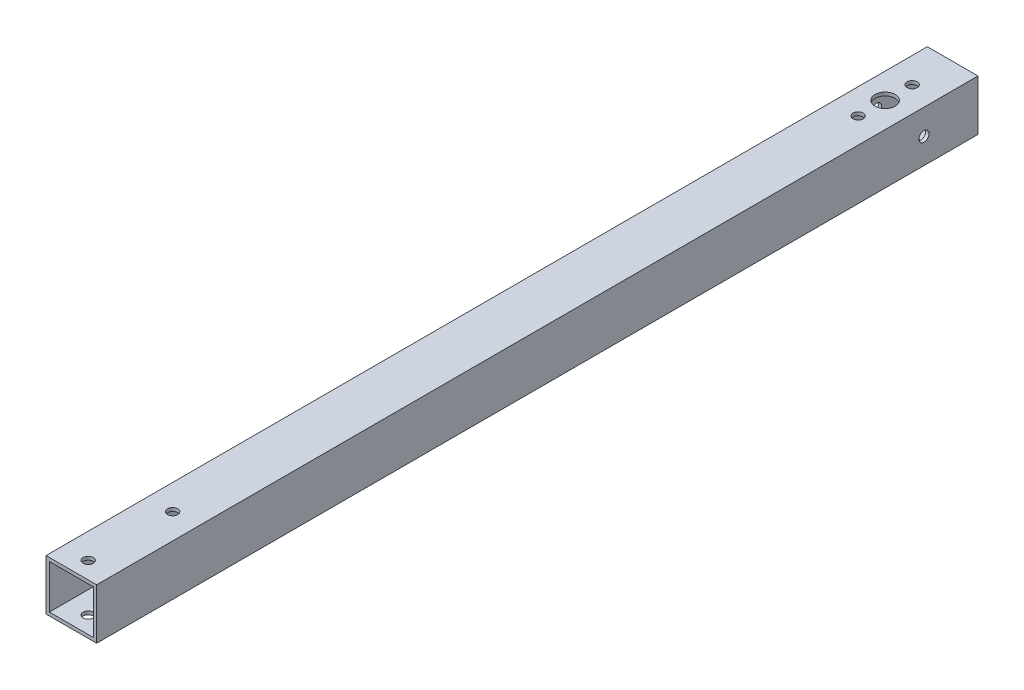
SolidWorks part; units mm, degrees
material "1060 Alloy"
ref_plane "Front Plane" through (0, 0, 0) normal (0, 0, 1) x (1, 0, 0)
ref_plane "Top Plane" through (0, 0, 0) normal (0, 1, 0) x (1, 0, 0)
ref_plane "Right Plane" through (0, 0, 0) normal (1, 0, 0) x (0, 0, -1)
sketch "Sketch1" plane through (0, 0, 0) normal (0, 0, 1) x (1, 0, 0)
  line L1 (-44.2961, 22.1481) -> (-29.2961, 22.1481)
  line L2 (-44.2961, 22.1481) -> (-44.2961, 7.1481)
  line L3 (-44.2961, 7.1481) -> (-29.2961, 7.1481)
  line L4 (-29.2961, 22.1481) -> (-29.2961, 7.1481)
  dimension "D1" = 15
  dimension "D2" = 15
extrude "Boss-Extrude1" add sketch "Sketch1" along normal blind 261
sketch "Sketch2" plane through (0, 0, 0) normal (0, 0, -1) x (-1, 0, 0)
  line L0 (29.2961, 7.1481) -> (29.2961, 22.1481) construction
  line L1 (30.2961, 21.1481) -> (43.2961, 21.1481)
  line L2 (30.2961, 21.1481) -> (30.2961, 8.1481)
  line L3 (30.2961, 8.1481) -> (43.2961, 8.1481)
  line L4 (43.2961, 21.1481) -> (43.2961, 8.1481)
  line L5 (29.2961, 22.1481) -> (44.2961, 22.1481) construction
  dimension "D1" = 13
  dimension "D2" = 1
  dimension "D3" = 1
extrude "Cut-Extrude1" cut sketch "Sketch2" against normal blind 261
hole_wizard "Ø3.0 (3) Diameter Hole1" positions "Sketch4" profile "Sketch3" hole size "Ø3.0" standard "ANSI Metric" end condition through all
sketch "Sketch4" plane through (0, 22.1481, 0) normal (0, 1, 0) x (1, 0, 0)
  line L0 (-29.2961, -261) -> (-44.2961, -261) construction
  line L1 (-29.2961, -261) -> (-29.2961, 0) construction
  point P0 (-36.7961, -256)
  point P2 (-36.7961, -231)
  dimension "D1" = 25
  dimension "D2" = 5
  dimension "D3" = 7.5
  dimension "D4" = 7.5
sketch "Sketch3" plane through (-36.7961, 22.1481, 256) normal (1, 0, 0) x (0, 0, 1)
  line L0 (0, 0) -> (0, 15)
  line L1 (0, 15) -> (1.5, 15)
  line L2 (1.5, 15) -> (1.5, 0)
  line L5 (1.5, 0) -> (0, 0)
  line L11 (0, -6.35) -> (0, 107.95) construction
  dimension "Thru Hole Dia." = 3
  dimension "Thru Hole Depth" = 15
hole_wizard "Ø3.0 (3) Diameter Hole2" positions "Sketch6" profile "Sketch5" hole size "Ø3.0" standard "ANSI Metric" end condition through all
sketch "Sketch6" plane through (0, 22.1481, 0) normal (0, 1, 0) x (1, 0, 0)
  line L0 (-29.2961, 0) -> (-44.2961, 0) construction
  line L1 (-44.2961, -261) -> (-44.2961, 0) construction
  point P0 (-36.7961, -12)
  point P2 (-36.7961, -28)
  point P5 (-36.7961, 0)
  dimension "D1" = 12
  dimension "D2" = 16
  dimension "D3" = 7.5
sketch "Sketch5" plane through (-36.7961, 22.1481, 12) normal (1, 0, 0) x (0, 0, 1)
  line L0 (0, 0) -> (0, 15)
  line L1 (0, 15) -> (1.5, 15)
  line L2 (1.5, 15) -> (1.5, 0)
  line L5 (1.5, 0) -> (0, 0)
  line L11 (0, -6.35) -> (0, 107.95) construction
  dimension "Thru Hole Dia." = 3
  dimension "Thru Hole Depth" = 15
hole_wizard "Ø6.0 (6) Diameter Hole1" positions "Sketch8" profile "Sketch7" hole size "Ø6.0" standard "ANSI Metric"
sketch "Sketch8" plane through (0, 22.1481, 0) normal (0, 1, 0) x (1, 0, 0)
  line L0 (-44.2961, -261) -> (-44.2961, 0) construction
  circle A0 centre (-36.7961, -12) radius 1.5 construction
  point P0 (-36.7961, -20)
  dimension "D2" = 8
  dimension "D1" = 7.5
sketch "Sketch7" plane through (-36.7961, 22.1481, 20) normal (1, 0, 0) x (0, 0, 1)
  line L0 (0, 0) -> (0, 11.8026)
  line L1 (0, 11.8026) -> (3, 10)
  line L2 (3, 10) -> (3, 0)
  line L5 (3, 0) -> (0, 0)
  line L10 (0, 11.8026) -> (-3, 10) construction
  line L11 (0, -6.35) -> (0, 107.95) construction
  dimension "Hole Dia." = 6
  dimension "Hole Depth" = 10
  dimension "Drill Angle" = 118
hole_wizard "Ø3.0 (3) Diameter Hole3" positions "Sketch10" profile "Sketch11" hole size "Ø3.0" standard "ANSI Metric" end condition through all
sketch "Sketch10" plane through (-44.2961, 0, 0) normal (-1, 0, 0) x (0, 0, 1)
  line L0 (261, 22.1481) -> (0, 22.1481) construction
  line L1 (0, 22.1481) -> (0, 7.1481) construction
  point P0 (16, 14.6481)
  dimension "D1" = 7.5
  dimension "D2" = 16
sketch "Sketch11" plane through (-44.2961, 14.6481, 16) normal (0, 1, 0) x (0, 0, 1)
  line L0 (0, 0) -> (0, 15)
  line L1 (0, 15) -> (1.5, 15)
  line L2 (1.5, 15) -> (1.5, 0)
  line L5 (1.5, 0) -> (0, 0)
  line L11 (0, -6.35) -> (0, 107.95) construction
  dimension "Thru Hole Dia." = 3
  dimension "Thru Hole Depth" = 15
